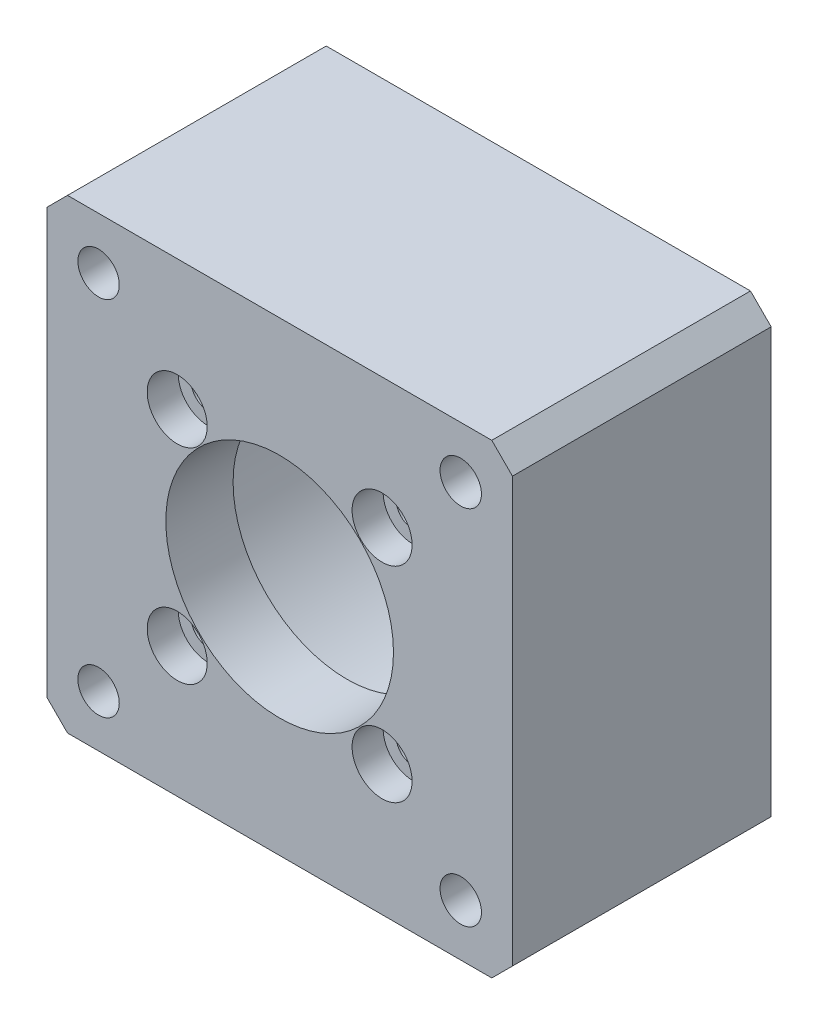
SolidWorks part; units mm, degrees
ref_plane "Front Plane" through (0, 0, 0) normal (0, 0, 1) x (1, 0, 0)
ref_plane "Top Plane" through (0, 0, 0) normal (0, 1, 0) x (1, 0, 0)
ref_plane "Right Plane" through (0, 0, 0) normal (1, 0, 0) x (0, 0, -1)
sketch "Sketch1" plane through (0, 0, 0) normal (0, 0, 1) x (1, 0, 0)
  line L1 (-22.5, 22.5) -> (22.5, 22.5)
  line L2 (-22.5, 22.5) -> (-22.5, -22.5)
  line L3 (-22.5, -22.5) -> (22.5, -22.5)
  line L4 (22.5, 22.5) -> (22.5, -22.5)
  line L5 (-22.5, 22.5) -> (22.5, -22.5) construction
  line L6 (-22.5, -22.5) -> (22.5, 22.5) construction
  circle A1 centre (-17.5, 17.5) radius 2
  circle A2 centre (17.5, 17.5) radius 2
  circle A3 centre (17.5, -17.5) radius 2
  circle A4 centre (-17.5, -17.5) radius 2
  point P18 (0, 0)
  dimension "D4" = 4
  dimension "D2" = 45
  dimension "D3" = 45
  dimension "D6" = 35
  dimension "D5" = 4
extrude "Boss-Extrude1" add sketch "Sketch1" along normal blind 25
sketch "Sketch2" plane through (0, 0, 25) normal (0, 0, 1) x (1, 0, 0)
  line L0 (0, 0) -> (17.5497, 0) construction
  line L1 (0, 0) -> (9.8995, 9.8995) construction
  circle A0 centre (9.8995, 9.8995) radius 1.65
  circle A1 centre (9.8995, -9.8995) radius 1.65
  circle A2 centre (-9.8995, -9.8995) radius 1.65
  circle A3 centre (-9.8995, 9.8995) radius 1.65
  circle A4 centre (0, 0) radius 11
  point P14 (0, 0)
  dimension "D2" = 3.3
  dimension "D1" = 45
  dimension "D3" = 14
  dimension "D4" = 4
extrude "Cut-Extrude1" cut sketch "Sketch2" against normal up to surface (25 mm away) up to face at (0, 0, 0)
sketch "Sketch3" plane through (0, 0, 25) normal (0, 0, 1) x (1, 0, 0)
  circle A0 centre (9.8995, 9.8995) radius 2.9
  circle A1 centre (9.8995, -9.8995) radius 2.9
  circle A2 centre (-9.8995, -9.8995) radius 2.9
  circle A3 centre (-9.8995, 9.8995) radius 2.9
  circle A4 centre (9.8995, -9.8995) radius 1.65 construction
  point P12 (0, 0)
  dimension "D1" = 5.8
  dimension "D2" = 4
extrude "Cut-Extrude2" cut sketch "Sketch3" against normal blind 3
chamfer "Chamfer1" distance 2 angle 45 4 edges at (-22.5, -22.5, 12.5) (22.5, -22.5, 12.5) (22.5, 22.5, 12.5) (-22.5, 22.5, 12.5)
sketch "Sketch4" plane through (0, 0, 0) normal (0, 0, -1) x (-1, 0, 0)
  circle A1 centre (0, 0) radius 18.15
  dimension "D1" = 36.3
extrude "Cut-Extrude3" cut sketch "Sketch4" against normal blind 18.5
ref_plane "基准面1" through (0, 0, 25) normal (0, 0, 1) x (1, 0, 0)
sketch "草图4" plane through (0, 0, 0) normal (0, 0, -1) x (-1, 0, 0)
  line L0 (-17.5, 13.3431) -> (-13.9, 15.4215)
  line L1 (-13.9, 15.4215) -> (-13.9, 19.5785)
  line L2 (-13.9, 19.5785) -> (-17.5, 21.6569)
  line L3 (-17.5, 21.6569) -> (-21.1, 19.5785)
  line L4 (-21.1, 19.5785) -> (-21.1, 15.4215)
  line L5 (-21.1, 15.4215) -> (-17.5, 13.3431)
  line L6 (-15.5, 17.5) -> (-17.5, 17.5) construction
  line L7 (17.5, 13.3431) -> (21.1, 15.4215)
  line L8 (21.1, 15.4215) -> (21.1, 19.5785)
  line L9 (21.1, 19.5785) -> (17.5, 21.6569)
  line L10 (17.5, 21.6569) -> (13.9, 19.5785)
  line L11 (13.9, 19.5785) -> (13.9, 15.4215)
  line L12 (13.9, 15.4215) -> (17.5, 13.3431)
  line L13 (19.5, 17.5) -> (17.5, 17.5) construction
  line L14 (-15.5, -17.5) -> (-17.5, -17.5) construction
  line L15 (19.5, -17.5) -> (17.5, -17.5) construction
  line L16 (19.5, 17.5) -> (17.5, 17.5)
  line L17 (17.5, -21.6569) -> (21.1, -19.5785)
  line L18 (21.1, -19.5785) -> (21.1, -15.4215)
  line L19 (21.1, -15.4215) -> (17.5, -13.3431)
  line L20 (17.5, -13.3431) -> (13.9, -15.4215)
  line L21 (13.9, -15.4215) -> (13.9, -19.5785)
  line L22 (13.9, -19.5785) -> (17.5, -21.6569)
  line L23 (19.5, -17.5) -> (17.5, -17.5)
  line L24 (-17.5, -21.6569) -> (-13.9, -19.5785)
  line L25 (-13.9, -19.5785) -> (-13.9, -15.4215)
  line L26 (-13.9, -15.4215) -> (-17.5, -13.3431)
  line L27 (-17.5, -13.3431) -> (-21.1, -15.4215)
  line L28 (-21.1, -15.4215) -> (-21.1, -19.5785)
  line L29 (-21.1, -19.5785) -> (-17.5, -21.6569)
  line L30 (-15.5, -17.5) -> (-17.5, -17.5)
  circle A0 centre (-17.5, 17.5) radius 3.6 construction
  circle A1 centre (-17.5, 17.5) radius 2 construction
  circle A2 centre (17.5, 17.5) radius 3.6 construction
  circle A3 centre (-17.5, -17.5) radius 2 construction
  circle A4 centre (17.5, -17.5) radius 2 construction
  circle A5 centre (17.5, 17.5) radius 2 construction
  circle A6 centre (17.5, -17.5) radius 3.6 construction
  circle A7 centre (-17.5, -17.5) radius 3.6 construction
  circle M27 centre (17.5, 17.5) radius 2
  circle M28 centre (-17.5, 17.5) radius 2
  circle M29 centre (-17.5, -17.5) radius 2
  circle M30 centre (17.5, -17.5) radius 2
  dimension "D1" = 7.2
extrude "切除-拉伸10" cut sketch "草图4" against normal blind 4 contours L11 L12 L7 L8 L9 L10 M27 | L4 L5 L0 L1 L2 L3 M28 | L28 L29 L24 L25 L26 L27 M29 | L21 L22 L17 L18 L19 L20 M30
